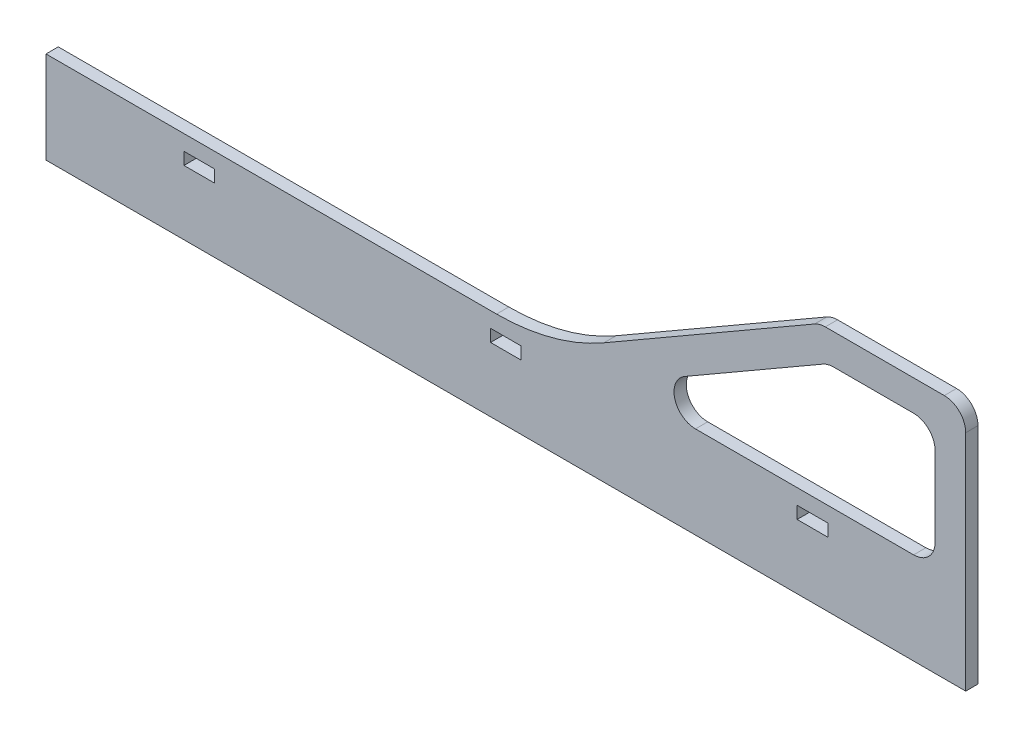
SolidWorks part; units mm, degrees
ref_plane "Piano frontale" through (0, 0, 0) normal (0, 0, 1) x (1, 0, 0)
ref_plane "Piano superiore" through (0, 0, 0) normal (0, 1, 0) x (1, 0, 0)
ref_plane "Piano destro" through (0, 0, 0) normal (1, 0, 0) x (0, 0, -1)
sketch "Schizzo1" plane through (0, 0, 0) normal (0, 0, 1) x (1, 0, 0)
  line L0 (400, 30) -> (400, 0)
  line L1 (400, 0) -> (700, 0)
  line L3 (400, 30) -> (546.9591, 30)
  line L4 (700, 0) -> (700, 30)
  line L5 (445, 21) -> (455, 21)
  line L6 (445, 21) -> (445, 25)
  line L7 (445, 25) -> (455, 25)
  line L8 (455, 21) -> (455, 25)
  line L9 (545, 21) -> (555, 21)
  line L10 (545, 21) -> (545, 25)
  line L11 (545, 25) -> (555, 25)
  line L12 (645, 21) -> (655, 21)
  line L13 (645, 21) -> (645, 25)
  line L14 (645, 25) -> (655, 25)
  line L15 (655, 21) -> (655, 25)
  line L16 (555, 21) -> (555, 25)
  line L32 (654.1937, 80) -> (693, 80)
  line L34 (700, 73) -> (700, 30)
  line L35 (650.6937, 79.0622) -> (581.9591, 39.3782)
  line L36 (690, 63) -> (690, 37)
  line L37 (656.8732, 70) -> (683, 70)
  line L38 (653.3732, 69.0622) -> (608.3399, 43.0622)
  line L39 (611.8399, 30) -> (683, 30)
  line L40 (654.9976, 70) -> (570.7156, 21.3397) construction
  line L41 (654.9976, 70) -> (690, 70) construction
  line L42 (690, 70) -> (690, 30) construction
  line L43 (652.3181, 80) -> (700, 80) construction
  line L44 (700, 80) -> (700, 30) construction
  line L45 (652.3181, 80) -> (565.7156, 30) construction
  arc A0 (611.8399, 30) -> (608.3399, 43.0622) centre (611.8399, 37) cw
  arc A1 (656.8732, 70) -> (653.3732, 69.0622) centre (656.8732, 63) ccw
  arc A2 (683, 30) -> (690, 37) centre (683, 37) ccw
  arc A3 (690, 63) -> (683, 70) centre (683, 63) ccw
  arc A4 (693, 80) -> (700, 73) centre (693, 73) cw
  arc A5 (654.1937, 80) -> (650.6937, 79.0622) centre (654.1937, 73) ccw
  arc A6 (581.9591, 39.3782) -> (546.9591, 30) centre (546.9591, 100) cw
  dimension "D11" = 30
  dimension "D13" = 7
  dimension "D14" = 70
  dimension "D10" = 21
  dimension "D12" = 10
  dimension "D15" = 153.0409
  dimension "D16" = 43
  dimension "D21" = 10
  dimension "D17" = 26
  dimension "D18" = 4
  dimension "D2" = 30
  dimension "D3" = 300
  dimension "D4" = 45
  dimension "D5" = 4
  dimension "D6" = 10
  dimension "D8" = 79.3679
  dimension "D9" = 90
  dimension "D19" = 400
  dimension "D20" = 10
  dimension "D22" = 90
  dimension "D23" = 5
  dimension "D24" = 21
  dimension "D7" = 21
extrude "Estrusione-Estrusione3" add sketch "Schizzo1" along normal blind 4
